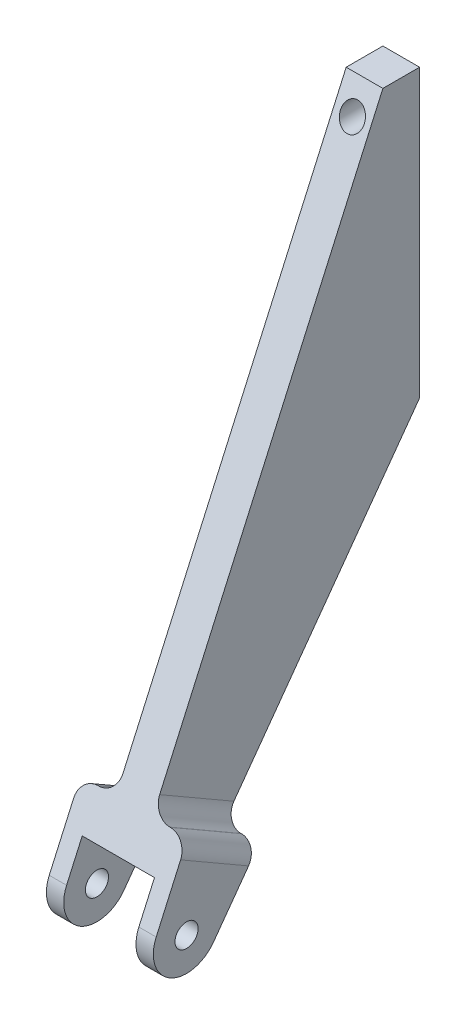
SolidWorks part; units mm, degrees
ref_plane "Front Plane" through (0, 0, 0) normal (0, 0, 1) x (1, 0, 0)
ref_plane "Top Plane" through (0, 0, 0) normal (0, 1, 0) x (1, 0, 0)
ref_plane "Right Plane" through (0, 0, 0) normal (1, 0, 0) x (0, 0, -1)
sketch "Sketch1" plane through (0, 0, 0) normal (0, 0, 1) x (1, 0, 0)
  line L1 (-72.0584, -12.4142) -> (-72.0584, -329.7013) construction
  line L4 (-78.4084, -322.2124) -> (-65.7084, -322.2124)
  line L5 (-78.4084, -322.2124) -> (-78.4084, -2.8892)
  line L6 (-78.4084, -2.8892) -> (-65.7084, -2.8892)
  line L7 (-65.7084, -322.2124) -> (-65.7084, -2.8892)
  line L8 (-78.4084, -322.2124) -> (-65.7084, -2.8892) construction
  line L9 (-78.4084, -2.8892) -> (-65.7084, -322.2124) construction
  point P0 (-72.0584, -162.5508)
  dimension "D1" = 12.7
extrude "Boss-Extrude1" add sketch "Sketch1" along normal blind 112.776
sketch "Sketch2" plane through (-65.7084, 0, 0) normal (1, 0, 0) x (0, 0, -1)
  line L0 (0, -102) -> (-83.4596, -217.2296)
  line L1 (0, -322.2124) -> (0, -2.8892) construction
  line L2 (0, -2.8892) -> (-12.7, -2.8892)
  line L3 (-112.776, -2.8892) -> (0, -2.8892) construction
  line L4 (19.05, -102) -> (0, -102) construction
  line L5 (-12.7, -2.8892) -> (-103.2746, -205.7962)
  line L6 (0, -102) -> (0, -2.8892)
  line L8 (-143.9151, -343.6077) -> (30.3223, -343.6077)
  line L9 (-143.9151, -343.6077) -> (-143.9151, 9.7561)
  line L10 (-143.9151, 9.7561) -> (30.3223, 9.7561)
  line L11 (30.3223, -343.6077) -> (30.3223, 9.7561)
  circle A0 centre (9.525, -112) radius 142 construction
  circle A5 centre (9.525, -112) radius 142 construction
  arc A6 (-103.2746, -205.7962) -> (-83.4596, -217.2296) centre (-92.7733, -210.4838) ccw
  circle A7 centre (-92.7733, -210.4838) radius 4
  dimension "D4" = 23
  dimension "D5" = 8
  dimension "D1" = 12.7
extrude "Cut-Extrude1" cut sketch "Sketch2" against normal through all
sketch "Sketch3" plane through (0, 0, 0) normal (0, 0, -1) x (-1, 0, 0)
  line L0 (72, -12.4142) -> (72, -91.7892) construction
  circle A0 centre (72, -12.4142) radius 4.1275
  circle A1 centre (72, -91.7892) radius 4.1275
  dimension "D1" = 79.375
  dimension "D2" = 8.255
extrude "Cut-Extrude2" cut sketch "Sketch3" against normal blind 25.4
ref_plane "Plane1" through (-72.0584, 0, 0) normal (1, 0, 0) x (0, 0, -1)
sketch "Sketch4" plane through (-72.0584, 0, 0) normal (1, 0, 0) x (0, 0, -1)
  line L1 (-12.7, -2.8892) -> (-103.2746, -205.7962) construction
  line L5 (-67.7794, -195.5804) -> (-92.3785, -181.3865)
  line L6 (0, -102) -> (-83.4596, -217.2296) construction
  line L8 (-92.7733, -210.4838) -> (-80.0789, -188.4835) construction
  line L10 (-83.4596, -217.2296) -> (-67.7794, -195.5804)
  line L11 (-103.2746, -205.7962) -> (-92.3785, -181.3865)
  circle A2 centre (-92.7733, -210.4838) radius 4 construction
  circle A3 centre (-92.7733, -210.4838) radius 4
  arc A4 (-103.2746, -205.7962) -> (-83.4596, -217.2296) centre (-92.7733, -210.4838) ccw construction
  arc A5 (-103.2746, -205.7962) -> (-83.4596, -217.2296) centre (-92.7733, -210.4838) ccw
  point P1 (-63.9369, -190.2753)
  point P3 (-78.1905, -208.5677)
  point P9 (-51.4385, -207.6173)
  point P10 (-79.9354, -188.5413)
  point P11 (-67.7793, -195.5804)
  dimension "D2" = 25.4
extrude "Boss-Extrude2" add sketch "Sketch4" along normal mid plane 37
sketch "Sketch6" plane through (-72.0584, 0, 0) normal (1, 0, 0) x (0, 0, -1)
  line L0 (-102.8827, -190.7962) -> (-56.5696, -217.5193)
  line L1 (-56.5696, -217.5193) -> (-85.0862, -269.6791)
  line L2 (-85.0862, -269.6791) -> (-153.8338, -230.3279)
  line L3 (-153.8338, -230.3279) -> (-102.8827, -190.7962)
  line L5 (-67.7794, -195.5804) -> (-92.3785, -181.3865) construction
  circle A0 centre (-92.7733, -210.4838) radius 4 construction
  circle A1 centre (-92.7733, -210.4838) radius 4 construction
  dimension "D1" = 12
extrude "Cut-Extrude3" cut sketch "Sketch6" against normal mid plane 25
fillet "Fillet1" radius 6 4 edges at (-90.5584, -188.4835, 80.0789) (-78.4084, -188.4835, 80.0789) (-53.5584, -188.4835, 80.0789) (-65.7084, -188.4835, 80.0789)
